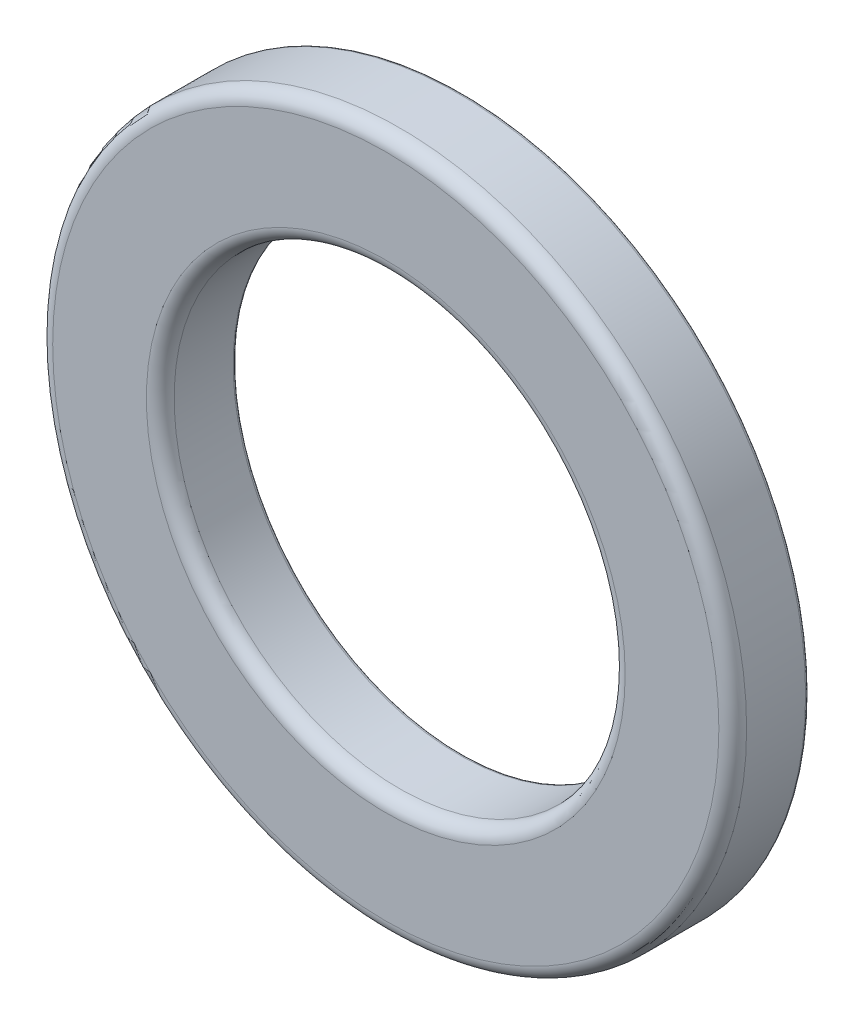
SolidWorks part; units mm, degrees
ref_plane "Front Plane" through (0, 0, 0) normal (0, 0, 1) x (1, 0, 0)
ref_plane "Top Plane" through (0, 0, 0) normal (0, 1, 0) x (1, 0, 0)
ref_plane "Right Plane" through (0, 0, 0) normal (1, 0, 0) x (0, 0, -1)
sketch "Sketch1" plane through (0, 0, 0) normal (0, 0, 1) x (1, 0, 0)
  circle A0 centre (0, 0) radius 10 construction
  circle A1 centre (0, 0) radius 6.5 construction
  point P5 (0, -10)
  dimension "OD" = 20
  dimension "ID" = 13
sketch "Sketch2" plane through (0, 0, 0) normal (1, 0, 0) x (0, 0, -1)
  line L0 (0.9, 0) -> (-0.9, 0) construction
  line L1 (-1.1, -10) -> (1.1, -10) construction
  point P0 (-1.1, -10)
  point P3 (1.1, -10)
  point P4 (0, 0)
  point P9 (0, -10)
  point P10 (0.9, -10)
  point P11 (-1.1, -10)
  point P12 (-0.9, -10)
  point P13 (1.1, -10)
  dimension "Thickness Range [Min]" = 1.8
  dimension "Thickness Range [Max]" = 2.2
sketch "Sketch3" plane through (0, 0, 0) normal (0, 0, 1) x (1, 0, 0)
  circle A0 centre (0, 0) radius 6.5 construction
  circle A1 centre (0, 0) radius 10 construction
  circle A2 centre (0, 0) radius 6.5
  circle A3 centre (0, 0) radius 10
extrude "Boss-Extrude1" add sketch "Sketch3" against normal up to vertex (1.1 mm away) and the other way up to vertex (1.1 mm away) up to point (0, -10, -1.1) other way up to point (0, -10, 1.1)
fillet "Fillet1" radius 0.4 2 edges at (6.5, 0, 1.1) (10, 0, 1.1)
fillet "Fillet2" radius 0.1 2 edges at (10, 0, -1.1) (6.5, 0, -1.1)
equation "\"D1@Fillet1\"=\"OD@Sketch1\"*.02"
equation "\"D1@Fillet2\"=\"OD@Sketch1\"*.005"
